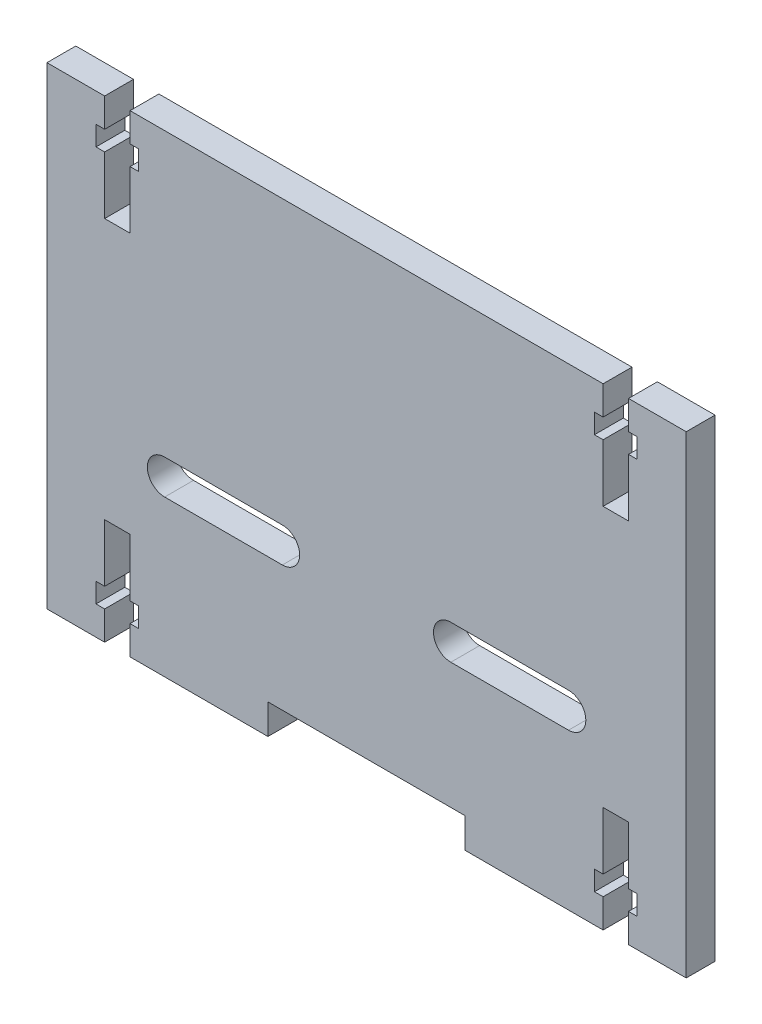
SolidWorks part; units mm, degrees
ref_plane "Front Plane" through (0, 0, 0) normal (0, 0, 1) x (1, 0, 0)
ref_plane "Top Plane" through (0, 0, 0) normal (0, 1, 0) x (1, 0, 0)
ref_plane "Right Plane" through (0, 0, 0) normal (1, 0, 0) x (0, 0, -1)
sketch "Sketch1" plane through (0, 0, 0) normal (0, 0, 1) x (1, 0, 0)
  line L1 (-55.4, 41) -> (55.4, 41)
  line L2 (-55.4, 41) -> (-55.4, -41)
  line L3 (-55.4, -41) -> (55.4, -41)
  line L4 (55.4, 41) -> (55.4, -41)
  dimension "D1" = 110.8
  dimension "D2" = 55.4
  dimension "D3" = 82
  dimension "D4" = 41
extrude "Boss-Extrude1" add sketch "Sketch1" along normal blind 5
sketch "Sketch2" plane through (0, 0, 5) normal (0, 0, 1) x (1, 0, 0)
  line L0 (43.2, -20.8) -> (43.2, -35.6452) construction
  line L13 (41, -32.6) -> (41, -22.6)
  line L14 (-55.4, 41) -> (-55.4, -41) construction
  line L15 (0, 0) -> (-49.1489, 0) construction
  line L16 (0, 0) -> (0, 26.0159) construction
  line L17 (45.4, -36) -> (45.4, -41)
  line L30 (0, 0) -> (0, 10.9555) construction
  line L43 (39.5, -36) -> (41, -36)
  line L80 (-43.2, 20.8) -> (-43.2, 35.6452) construction
  line L81 (-41, 32.6) -> (-41, 22.6)
  line L82 (-45.4, 36) -> (-45.4, 41)
  line L83 (-39.5, 36) -> (-41, 36)
  line L84 (-39.5, 32.6) -> (-39.5, 36)
  line L85 (-41, 32.6) -> (-39.5, 32.6)
  line L86 (-46.9, 36) -> (-45.4, 36)
  line L87 (-46.9, 32.6) -> (-46.9, 36)
  line L88 (-45.4, 32.6) -> (-46.9, 32.6)
  line L89 (-45.4, 22.6) -> (-41, 22.6)
  line L90 (-41, 41) -> (-41, 36)
  line L91 (-45.4, 41) -> (-41, 41)
  line L92 (-45.4, 22.6) -> (-45.4, 32.6)
  line L93 (55.4, 41) -> (-55.4, 41) construction
  line L94 (43.2, 20.8) -> (43.2, 35.6452) construction
  line L95 (45.4, 22.6) -> (45.4, 32.6)
  line L96 (45.4, 41) -> (41, 41)
  line L97 (41, 41) -> (41, 36)
  line L98 (45.4, 22.6) -> (41, 22.6)
  line L99 (45.4, 32.6) -> (46.9, 32.6)
  line L100 (46.9, 32.6) -> (46.9, 36)
  line L101 (46.9, 36) -> (45.4, 36)
  line L102 (41, 32.6) -> (39.5, 32.6)
  line L103 (39.5, 32.6) -> (39.5, 36)
  line L104 (39.5, 36) -> (41, 36)
  line L105 (45.4, 36) -> (45.4, 41)
  line L106 (41, 32.6) -> (41, 22.6)
  line L107 (39.5, -32.6) -> (39.5, -36)
  line L108 (41, -32.6) -> (39.5, -32.6)
  line L109 (46.9, -36) -> (45.4, -36)
  line L110 (46.9, -32.6) -> (46.9, -36)
  line L111 (45.4, -32.6) -> (46.9, -32.6)
  line L112 (45.4, -22.6) -> (41, -22.6)
  line L113 (41, -41) -> (41, -36)
  line L114 (45.4, -41) -> (41, -41)
  line L115 (45.4, -22.6) -> (45.4, -32.6)
  line L116 (-43.2, -20.8) -> (-43.2, -35.6452) construction
  line L117 (-45.4, -22.6) -> (-45.4, -32.6)
  line L118 (-45.4, -41) -> (-41, -41)
  line L119 (-41, -41) -> (-41, -36)
  line L120 (-45.4, -22.6) -> (-41, -22.6)
  line L121 (-45.4, -32.6) -> (-46.9, -32.6)
  line L122 (-46.9, -32.6) -> (-46.9, -36)
  line L123 (-46.9, -36) -> (-45.4, -36)
  line L124 (-41, -32.6) -> (-39.5, -32.6)
  line L125 (-39.5, -32.6) -> (-39.5, -36)
  line L126 (-39.5, -36) -> (-41, -36)
  line L127 (-45.4, -36) -> (-45.4, -41)
  line L128 (-41, -32.6) -> (-41, -22.6)
  dimension "D10" = 5
  dimension "D11" = 3.4
  dimension "D12" = 10
  dimension "D13" = 2.2
  dimension "D14" = 4.4
  dimension "D15" = 1.5
  dimension "D16" = 1.5
  dimension "D17" = 10
extrude "Cut-Extrude1" cut sketch "Sketch2" against normal blind 10
sketch "Sketch3" plane through (0, 0, 5) normal (0, 0, 1) x (1, 0, 0)
  line L4 (-17.1, -41) -> (17.1, -41)
  line L5 (17.1, -41) -> (17.1, -35.8)
  line L6 (-17.1, -41) -> (-17.1, -35.8)
  line L7 (17.1, -35.8) -> (-17.1, -35.8)
  line L8 (0, 0) -> (0, -50.9361) construction
  line L10 (-41, -41) -> (41, -41) construction
  dimension "D1" = 5.2
  dimension "D2" = 34.2
  dimension "D3" = 17.1
extrude "Cut-Extrude2" cut sketch "Sketch3" against normal blind 10
sketch "Sketch4" plane through (0, 0, 5) normal (0, 0, 1) x (1, 0, 0)
  line L2 (35, -14) -> (14.6, -14)
  line L3 (14.6, -8) -> (35, -8)
  line L4 (0, 0) -> (0, -28.7983) construction
  line L5 (-14.6, -8) -> (-35, -8)
  line L6 (-35, -14) -> (-14.6, -14)
  arc A2 (14.6, -8) -> (14.6, -14) centre (14.6, -11) ccw
  arc A3 (35, -14) -> (35, -8) centre (35, -11) ccw
  arc A4 (-35, -14) -> (-35, -8) centre (-35, -11) cw
  arc A5 (-14.6, -8) -> (-14.6, -14) centre (-14.6, -11) cw
extrude "Cut-Extrude3" cut sketch "Sketch4" against normal blind 10
